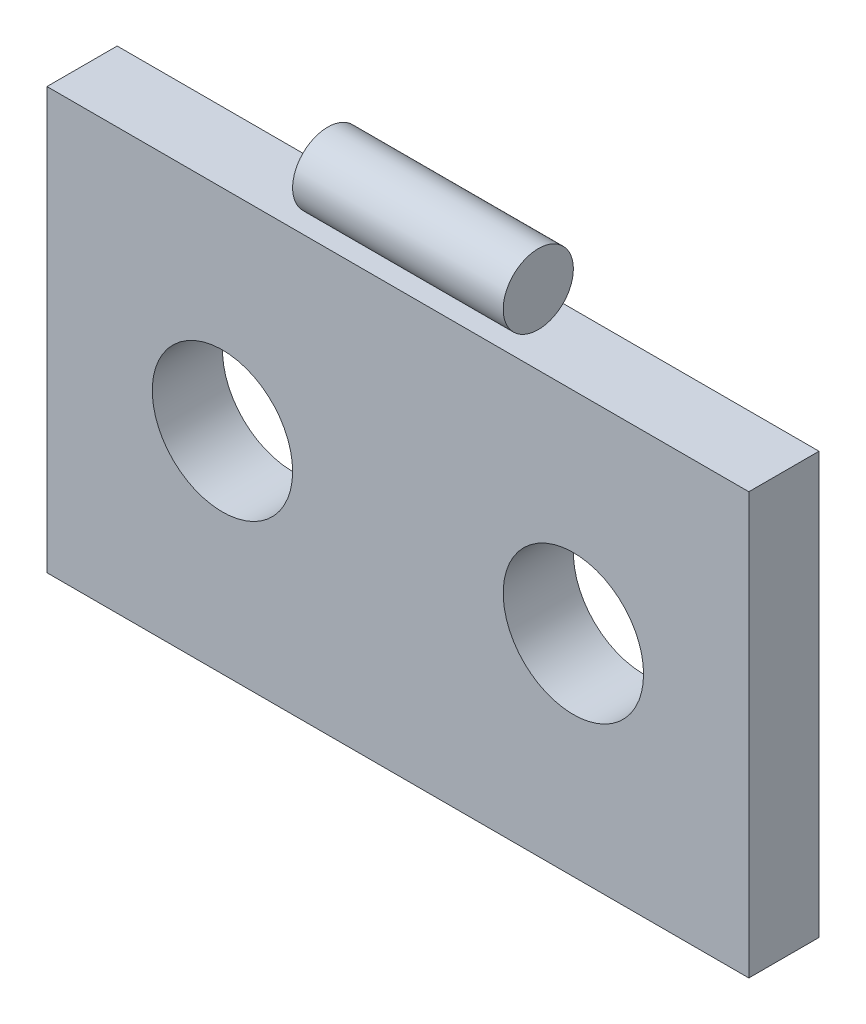
SolidWorks part; units mm, degrees
ref_plane "Plan de face" through (0, 0, 0) normal (0, 0, 1) x (1, 0, 0)
ref_plane "Plan de dessus" through (0, 0, 0) normal (0, 1, 0) x (1, 0, 0)
ref_plane "Plan de droite" through (0, 0, 0) normal (1, 0, 0) x (0, 0, -1)
sketch "Esquisse1" plane through (0, 0, 0) normal (0, 0, 1) x (1, 0, 0)
  line L1 (0, 0) -> (50, 0)
  line L2 (0, 0) -> (0, 30)
  line L3 (0, 30) -> (50, 30)
  line L4 (50, 0) -> (50, 30)
  dimension "D1" = 50
  dimension "D2" = 30
extrude "Boss.-Extru.1" add sketch "Esquisse1" along normal blind 5
sketch "Esquisse2" plane through (0, 0, 5) normal (0, 0, 1) x (1, 0, 0)
  line L0 (0, 15) -> (12.5, 15) construction
  line L1 (0, 30) -> (0, 0) construction
  line L2 (50, 15) -> (37.5, 15) construction
  line L3 (50, 0) -> (50, 30) construction
  circle A0 centre (12.5, 15) radius 5
  circle A1 centre (37.5, 15) radius 5
extrude "Enlèv. mat.-Extru.1" cut sketch "Esquisse2" against normal through all
sketch "Esquisse3" plane through (50, 0, 0) normal (1, 0, 0) x (0, 0, -1)
  line L0 (-2.5, 30) -> (-2.5, 32.5) construction
  line L1 (-5, 30) -> (0, 30) construction
  circle A0 centre (-2.5, 32.5) radius 2.5
  dimension "D1" = 2.5
extrude "Boss.-Extru.2" add sketch "Esquisse3" against normal blind 50 separate body
sketch "Esquisse5" plane through (0, 0, 5) normal (0, 0, 1) x (1, 0, 0)
  line L0 (17.5, 15) -> (17.5, 30) construction
  line L1 (50, 30) -> (0, 30) construction
  line L2 (32.5, 15) -> (32.5, 30) construction
  line L4 (17.5, 30) -> (0, 30)
  line L5 (17.5, 30) -> (17.5, 35)
  line L6 (17.5, 35) -> (0, 35)
  line L7 (0, 30) -> (0, 35)
  line L8 (32.5, 30) -> (50, 30)
  line L9 (32.5, 30) -> (32.5, 35)
  line L10 (32.5, 35) -> (50, 35)
  line L11 (50, 30) -> (50, 35)
  circle A0 centre (12.5, 15) radius 5 construction
  circle A1 centre (37.5, 15) radius 5 construction
  line M6 (50, 30) -> (0, 30)
extrude "Enlèv. mat.-Extru.6" cut sketch "Esquisse5" against normal through all contours L7 L5 L6 M6 | L11 L10 L9 M6
